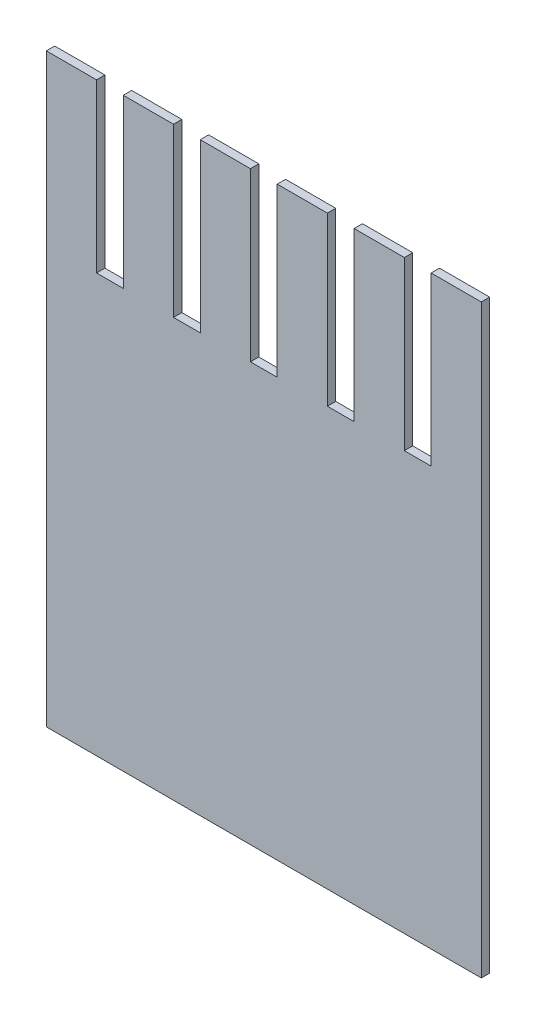
SolidWorks part; units mm, degrees
ref_plane "前视基准面" through (0, 0, 0) normal (0, 0, 1) x (1, 0, 0)
ref_plane "上视基准面" through (0, 0, 0) normal (0, 1, 0) x (1, 0, 0)
ref_plane "右视基准面" through (0, 0, 0) normal (1, 0, 0) x (0, 0, -1)
other "Configuration Table"
sketch "Sketch1" plane through (0, 0, 0) normal (0, 0, 1) x (1, 0, 0)
  line L0 (0, 25) -> (26, 25)
  line L1 (0, 0) -> (26, 0)
  line L2 (0, 0) -> (0, 35)
  line L3 (0, 35) -> (26, 35)
  line L4 (26, 0) -> (26, 35)
  line L5 (4.6, 35) -> (7.6, 35)
  line L6 (0, 35) -> (3, 35)
  line L7 (0, 35) -> (0, 25)
  line L8 (0, 25) -> (3, 25)
  line L9 (3, 35) -> (3, 25)
  line L10 (4.6, 35) -> (4.6, 25)
  line L11 (4.6, 25) -> (7.6, 25)
  line L12 (7.6, 35) -> (7.6, 25)
  line L13 (9.2, 35) -> (12.2, 35)
  line L14 (9.2, 35) -> (9.2, 25)
  line L15 (9.2, 25) -> (12.2, 25)
  line L16 (12.2, 35) -> (12.2, 25)
  line L17 (13.8, 35) -> (16.8, 35)
  line L18 (13.8, 35) -> (13.8, 25)
  line L19 (13.8, 25) -> (16.8, 25)
  line L20 (16.8, 35) -> (16.8, 25)
  line L21 (18.4, 35) -> (21.4, 35)
  line L22 (18.4, 35) -> (18.4, 25)
  line L23 (18.4, 25) -> (21.4, 25)
  line L24 (21.4, 35) -> (21.4, 25)
  line L25 (23, 35) -> (26, 35)
  line L26 (23, 35) -> (23, 25)
  line L27 (23, 25) -> (26, 25)
  line L28 (26, 35) -> (26, 25)
  dimension "D1" = 26
  dimension "D2" = 35
  dimension "D3" = 25
  dimension "D4" = 3
  dimension "D5" = 6
extrude "Boss-Extrude1" add sketch "Sketch1" along normal blind 0.5 contours L1 L4 L0 L2 | L9 L3 L2 L0 | L12 L3 L10 L0 | L16 L3 L14 L0 | L20 L3 L18 L0 | L24 L3 L22 L0 | L3 L26 L0 L4
